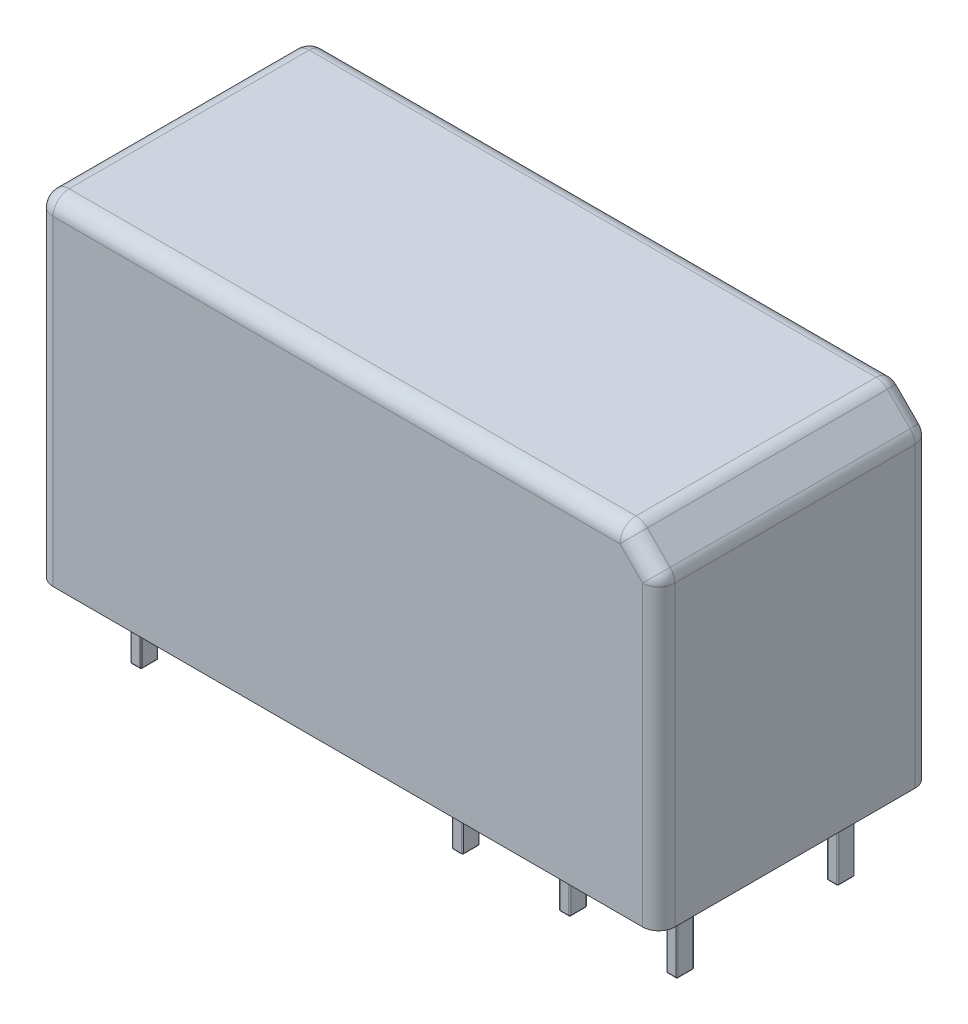
SolidWorks part; units mm, degrees
ref_plane "Спереди" through (0, 0, 0) normal (0, 0, 1) x (1, 0, 0)
ref_plane "Сверху" through (0, 0, 0) normal (0, 1, 0) x (1, 0, 0)
ref_plane "Справа" through (0, 0, 0) normal (1, 0, 0) x (0, 0, -1)
sketch "Эскиз1" plane through (0, 0, 0) normal (0, 1, 0) x (1, 0, 0)
  line L1 (-14.5, -6.35) -> (14.5, -6.35)
  line L2 (-14.5, -6.35) -> (-14.5, 6.35)
  line L3 (-14.5, 6.35) -> (14.5, 6.35)
  line L4 (14.5, -6.35) -> (14.5, 6.35)
  line L5 (-14.5, -6.35) -> (14.5, 6.35) construction
  line L6 (-14.5, 6.35) -> (14.5, -6.35) construction
  point P0 (0, 0)
  dimension "D1" = 29
  dimension "D2" = 12.7
extrude "Бобышка-Вытянуть1" add sketch "Эскиз1" along normal blind 15.7
sketch "Эскиз2" plane through (0, 0, 0) normal (0, -1, 0) x (1, 0, 0)
  line L0 (-14.5, -6.35) -> (-14.5, 6.35) construction
  line L1 (-12.3, 4.15) -> (-11.9, 4.15)
  line L2 (-12.35, 4.1) -> (-12.35, 3.4)
  line L3 (-12.3, 3.35) -> (-11.9, 3.35)
  line L4 (-11.85, 4.1) -> (-11.85, 3.4)
  line L5 (-12.35, 4.15) -> (-11.85, 3.35) construction
  line L6 (-12.35, 3.35) -> (-11.85, 4.15) construction
  line L7 (-7.35, 4.1) -> (-7.35, 3.4) [skipped]
  line L8 (-6.85, 4.1) -> (-6.85, 3.4) [skipped]
  line L9 (-7.3, 4.15) -> (-6.9, 4.15) [skipped]
  line L10 (-7.3, 3.35) -> (-6.9, 3.35) [skipped]
  line L11 (-2.35, 4.1) -> (-2.35, 3.4) [skipped]
  line L12 (-1.85, 4.1) -> (-1.85, 3.4) [skipped]
  line L13 (-2.3, 4.15) -> (-1.9, 4.15) [skipped]
  line L14 (-2.3, 3.35) -> (-1.9, 3.35) [skipped]
  line L15 (2.65, 4.1) -> (2.65, 3.4)
  line L16 (3.15, 4.1) -> (3.15, 3.4)
  line L17 (2.7, 4.15) -> (3.1, 4.15)
  line L18 (2.7, 3.35) -> (3.1, 3.35)
  line L19 (7.65, 4.1) -> (7.65, 3.4)
  line L20 (8.15, 4.1) -> (8.15, 3.4)
  line L21 (7.7, 4.15) -> (8.1, 4.15)
  line L22 (7.7, 3.35) -> (8.1, 3.35)
  line L23 (12.65, 4.1) -> (12.65, 3.4)
  line L24 (13.15, 4.1) -> (13.15, 3.4)
  line L25 (12.7, 4.15) -> (13.1, 4.15)
  line L26 (12.7, 3.35) -> (13.1, 3.35)
  line L27 (-7.35, -3.4) -> (-7.35, -4.1) [skipped]
  line L28 (-6.85, -3.4) -> (-6.85, -4.1) [skipped]
  line L29 (-7.3, -3.35) -> (-6.9, -3.35) [skipped]
  line L30 (-7.3, -4.15) -> (-6.9, -4.15) [skipped]
  line L31 (-2.35, -3.4) -> (-2.35, -4.1) [skipped]
  line L32 (-1.85, -3.4) -> (-1.85, -4.1) [skipped]
  line L33 (-2.3, -3.35) -> (-1.9, -3.35) [skipped]
  line L34 (-2.3, -4.15) -> (-1.9, -4.15) [skipped]
  line L35 (2.65, -3.4) -> (2.65, -4.1)
  line L36 (3.15, -3.4) -> (3.15, -4.1)
  line L37 (2.7, -3.35) -> (3.1, -3.35)
  line L38 (2.7, -4.15) -> (3.1, -4.15)
  line L39 (7.65, -3.4) -> (7.65, -4.1)
  line L40 (8.15, -3.4) -> (8.15, -4.1)
  line L41 (7.7, -3.35) -> (8.1, -3.35)
  line L42 (7.7, -4.15) -> (8.1, -4.15)
  line L43 (12.65, -3.4) -> (12.65, -4.1)
  line L44 (13.15, -3.4) -> (13.15, -4.1)
  line L45 (12.7, -3.35) -> (13.1, -3.35)
  line L46 (12.7, -4.15) -> (13.1, -4.15)
  line L47 (-12.35, -3.4) -> (-12.35, -4.1)
  line L48 (-11.85, -3.4) -> (-11.85, -4.1)
  line L49 (-12.3, -3.35) -> (-11.9, -3.35)
  line L50 (-12.3, -4.15) -> (-11.9, -4.15)
  arc A0 (-12.35, 3.4) -> (-12.3, 3.35) centre (-12.3, 3.4) ccw
  arc A1 (-11.9, 3.35) -> (-11.85, 3.4) centre (-11.9, 3.4) ccw
  arc A2 (-11.9, 4.15) -> (-11.85, 4.1) centre (-11.9, 4.1) cw
  arc A3 (-12.3, 4.15) -> (-12.35, 4.1) centre (-12.3, 4.1) ccw
  arc A4 (-7.35, 3.4) -> (-7.3, 3.35) centre (-7.3, 3.4) ccw [skipped]
  arc A5 (-6.9, 3.35) -> (-6.85, 3.4) centre (-6.9, 3.4) ccw [skipped]
  arc A6 (-6.9, 4.15) -> (-6.85, 4.1) centre (-6.9, 4.1) cw [skipped]
  arc A7 (-7.3, 4.15) -> (-7.35, 4.1) centre (-7.3, 4.1) ccw [skipped]
  arc A8 (-2.35, 3.4) -> (-2.3, 3.35) centre (-2.3, 3.4) ccw [skipped]
  arc A9 (-1.9, 3.35) -> (-1.85, 3.4) centre (-1.9, 3.4) ccw [skipped]
  arc A10 (-1.9, 4.15) -> (-1.85, 4.1) centre (-1.9, 4.1) cw [skipped]
  arc A11 (-2.3, 4.15) -> (-2.35, 4.1) centre (-2.3, 4.1) ccw [skipped]
  arc A12 (2.65, 3.4) -> (2.7, 3.35) centre (2.7, 3.4) ccw
  arc A13 (3.1, 3.35) -> (3.15, 3.4) centre (3.1, 3.4) ccw
  arc A14 (3.1, 4.15) -> (3.15, 4.1) centre (3.1, 4.1) cw
  arc A15 (2.7, 4.15) -> (2.65, 4.1) centre (2.7, 4.1) ccw
  arc A16 (7.65, 3.4) -> (7.7, 3.35) centre (7.7, 3.4) ccw
  arc A17 (8.1, 3.35) -> (8.15, 3.4) centre (8.1, 3.4) ccw
  arc A18 (8.1, 4.15) -> (8.15, 4.1) centre (8.1, 4.1) cw
  arc A19 (7.7, 4.15) -> (7.65, 4.1) centre (7.7, 4.1) ccw
  arc A20 (12.65, 3.4) -> (12.7, 3.35) centre (12.7, 3.4) ccw
  arc A21 (13.1, 3.35) -> (13.15, 3.4) centre (13.1, 3.4) ccw
  arc A22 (13.1, 4.15) -> (13.15, 4.1) centre (13.1, 4.1) cw
  arc A23 (12.7, 4.15) -> (12.65, 4.1) centre (12.7, 4.1) ccw
  arc A24 (-7.35, -4.1) -> (-7.3, -4.15) centre (-7.3, -4.1) ccw [skipped]
  arc A25 (-6.9, -4.15) -> (-6.85, -4.1) centre (-6.9, -4.1) ccw [skipped]
  arc A26 (-6.9, -3.35) -> (-6.85, -3.4) centre (-6.9, -3.4) cw [skipped]
  arc A27 (-7.3, -3.35) -> (-7.35, -3.4) centre (-7.3, -3.4) ccw [skipped]
  arc A28 (-2.35, -4.1) -> (-2.3, -4.15) centre (-2.3, -4.1) ccw [skipped]
  arc A29 (-1.9, -4.15) -> (-1.85, -4.1) centre (-1.9, -4.1) ccw [skipped]
  arc A30 (-1.9, -3.35) -> (-1.85, -3.4) centre (-1.9, -3.4) cw [skipped]
  arc A31 (-2.3, -3.35) -> (-2.35, -3.4) centre (-2.3, -3.4) ccw [skipped]
  arc A32 (2.65, -4.1) -> (2.7, -4.15) centre (2.7, -4.1) ccw
  arc A33 (3.1, -4.15) -> (3.15, -4.1) centre (3.1, -4.1) ccw
  arc A34 (3.1, -3.35) -> (3.15, -3.4) centre (3.1, -3.4) cw
  arc A35 (2.7, -3.35) -> (2.65, -3.4) centre (2.7, -3.4) ccw
  arc A36 (7.65, -4.1) -> (7.7, -4.15) centre (7.7, -4.1) ccw
  arc A37 (8.1, -4.15) -> (8.15, -4.1) centre (8.1, -4.1) ccw
  arc A38 (8.1, -3.35) -> (8.15, -3.4) centre (8.1, -3.4) cw
  arc A39 (7.7, -3.35) -> (7.65, -3.4) centre (7.7, -3.4) ccw
  arc A40 (12.65, -4.1) -> (12.7, -4.15) centre (12.7, -4.1) ccw
  arc A41 (13.1, -4.15) -> (13.15, -4.1) centre (13.1, -4.1) ccw
  arc A42 (13.1, -3.35) -> (13.15, -3.4) centre (13.1, -3.4) cw
  arc A43 (12.7, -3.35) -> (12.65, -3.4) centre (12.7, -3.4) ccw
  arc A44 (-12.35, -4.1) -> (-12.3, -4.15) centre (-12.3, -4.1) ccw
  arc A45 (-11.9, -4.15) -> (-11.85, -4.1) centre (-11.9, -4.1) ccw
  arc A46 (-11.9, -3.35) -> (-11.85, -3.4) centre (-11.9, -3.4) cw
  arc A47 (-12.3, -3.35) -> (-12.35, -3.4) centre (-12.3, -3.4) ccw
  point P0 (-12.1, 3.75)
  point P8 (-14.5, 0)
  point P21 (-11.85, 3.75)
  dimension "D1" = 0.05
  dimension "D2" = 0.5
  dimension "D3" = 3.75
  dimension "D4" = 2.4
  dimension "D5" = 0.8
  dimension "D6" = 6
  dimension "D7" = 2
extrude "Бобышка-Вытянуть2" add sketch "Эскиз2" along normal blind 3.5
fillet "Скругление1" radius 0.05 64 edges at (-11.8646, -3.5, 3.3646) (-12.1, -3.5, 3.35) (-12.3354, -3.5, 3.3646) (-12.35, -3.5, 3.75) (-12.3354, -3.5, 4.1354) (-12.1, -3.5, 4.15) (-11.8646, -3.5, 4.1354) (-11.8646, -3.5, -4.1354) (-12.1, -3.5, -4.15) (-12.3354, -3.5, -4.1354) (-12.35, -3.5, -3.75) (-12.3354, -3.5, -3.3646) (-12.1, -3.5, -3.35) (-11.8646, -3.5, -3.3646) (13.1354, -3.5, 3.3646) (12.9, -3.5, 3.35) (12.6646, -3.5, 3.3646) (12.65, -3.5, 3.75) (12.6646, -3.5, 4.1354) (12.9, -3.5, 4.15) (13.1354, -3.5, 4.1354) (8.1354, -3.5, 3.3646) (7.9, -3.5, 3.35) (7.6646, -3.5, 3.3646) (7.65, -3.5, 3.75) (7.6646, -3.5, 4.1354) (7.9, -3.5, 4.15) (8.1354, -3.5, 4.1354) (3.1354, -3.5, 3.3646) (2.9, -3.5, 3.35) (2.6646, -3.5, 3.3646) (2.65, -3.5, 3.75) (2.6646, -3.5, 4.1354) (2.9, -3.5, 4.15) (3.1354, -3.5, 4.1354) (3.1354, -3.5, -4.1354) (2.9, -3.5, -4.15) (2.6646, -3.5, -4.1354) (2.65, -3.5, -3.75) (2.6646, -3.5, -3.3646) (2.9, -3.5, -3.35) (3.1354, -3.5, -3.3646) (8.1354, -3.5, -4.1354) (7.9, -3.5, -4.15) (7.6646, -3.5, -4.1354) (7.65, -3.5, -3.75) (7.6646, -3.5, -3.3646) (7.9, -3.5, -3.35) (8.1354, -3.5, -3.3646) (13.1354, -3.5, -4.1354) (12.9, -3.5, -4.15) (12.6646, -3.5, -4.1354) (12.65, -3.5, -3.75) (12.6646, -3.5, -3.3646) (12.9, -3.5, -3.35) (13.1354, -3.5, -3.3646) (-11.85, -3.5, 3.75) (-11.85, -3.5, -3.75) (13.15, -3.5, 3.75) (8.15, -3.5, 3.75) (3.15, -3.5, 3.75) (3.15, -3.5, -3.75) (8.15, -3.5, -3.75) (13.15, -3.5, -3.75)
chamfer "Фаска1" distance 1.5 angle 45 1 edges at (14.5, 15.7, 0)
fillet "Скругление2" radius 0.75 11 edges at (13.75, 14.95, -6.35) (-14.5, 7.85, 6.35) (-14.5, 7.85, -6.35) (14.5, 7.1, -6.35) (14.5, 7.1, 6.35) (13.75, 14.95, 6.35) (14.5, 14.2, 0) (13, 15.7, 0) (-0.75, 15.7, -6.35) (-14.5, 15.7, 0) (-0.75, 15.7, 6.35)
